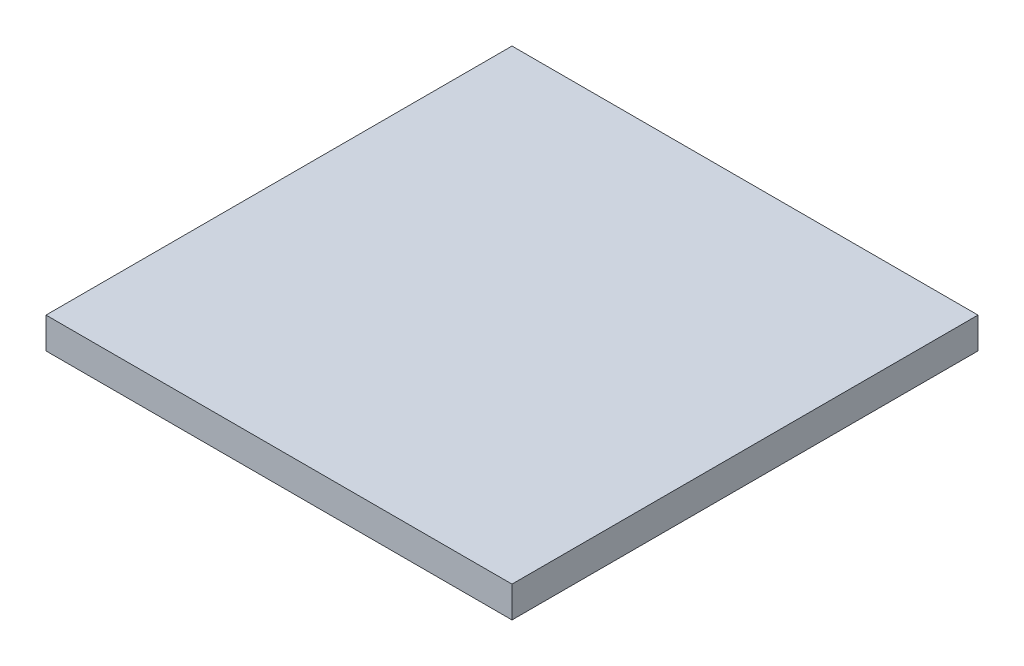
SolidWorks part; units mm, degrees
ref_plane "Front Plane" through (0, 0, 0) normal (0, 0, 1) x (1, 0, 0)
ref_plane "Top Plane" through (0, 0, 0) normal (0, 1, 0) x (1, 0, 0)
ref_plane "Right Plane" through (0, 0, 0) normal (1, 0, 0) x (0, 0, -1)
sketch "Sketch1" plane through (0, 0, 0) normal (0, 1, 0) x (1, 0, 0)
  line L1 (0, 0) -> (1524, 0)
  line L2 (0, 0) -> (0, 1524)
  line L3 (0, 1524) -> (1524, 1524)
  line L4 (1524, 0) -> (1524, 1524)
  dimension "D1" = 1524
  dimension "D2" = 1524
extrude "Boss-Extrude1" add sketch "Sketch1" along normal blind 101.6
